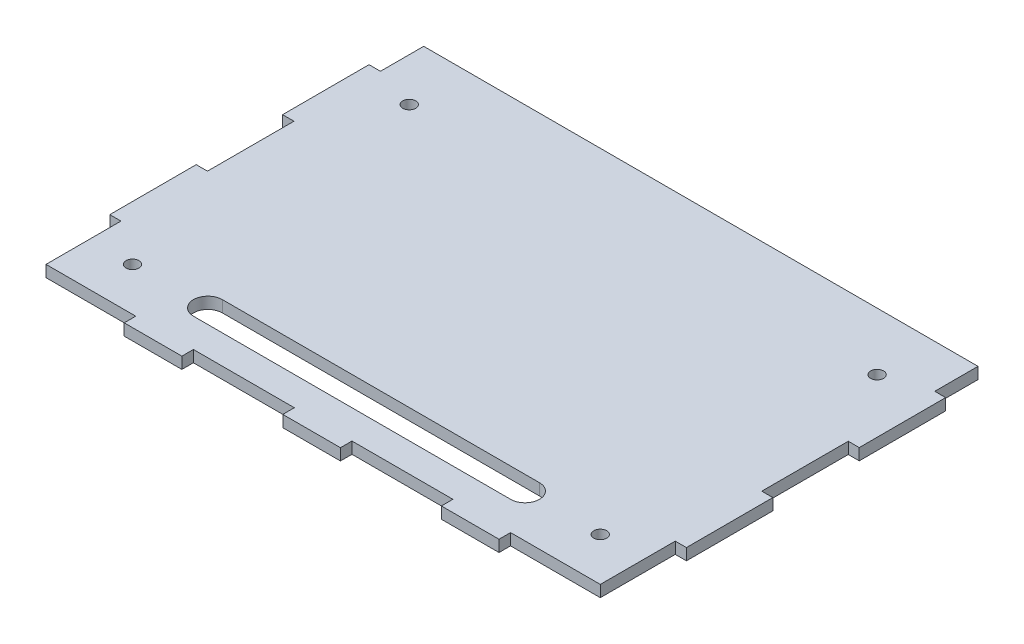
SolidWorks part; units mm, degrees
ref_plane "Plano frontal" through (0, 0, 0) normal (0, 0, 1) x (1, 0, 0)
ref_plane "Plano superior" through (0, 0, 0) normal (0, 1, 0) x (1, 0, 0)
ref_plane "Plano direito" through (0, 0, 0) normal (1, 0, 0) x (0, 0, -1)
sketch "Esboço1" plane through (0, 0, 0) normal (0, 1, 0) x (1, 0, 0)
  line L0 (-100.1571, 150) -> (-100.0001, 0)
  line L1 (-100.0001, 0) -> (100.0001, 0)
  line L2 (100.0001, 0) -> (99.843, 150)
  line L4 (99.843, 150) -> (-100.1571, 150)
  point P7 (0, 0)
  dimension "D1" = 200
  dimension "D2" = 150
extrude "Ressalto-extrusão1" add sketch "Esboço1" along normal blind 4
sketch "Esboço2" plane through (0, 4, 0) normal (0, 1, 0) x (1, 0, 0)
  line L0 (-65.0315, 0) -> (-65.0315, 4)
  line L1 (-100.0001, 0) -> (100.0001, 0) construction
  line L2 (-65.0315, 4) -> (-45.0315, 4)
  line L3 (-45.0315, 4) -> (-45.0315, 0)
  line L4 (-45.0315, 0) -> (-10.0315, 0)
  line L5 (-10.0315, 0) -> (-10.0315, 4)
  line L6 (-10.0315, 4) -> (9.9685, 4)
  line L7 (99.9685, 30) -> (99.9685, 4)
  line L8 (-100.1571, 150) -> (-100.0001, 0) construction
  line L9 (96.0942, 4) -> (99.9685, 4)
  line L10 (100.0942, 146) -> (100.0942, 150)
  line L13 (-65.0315, 4) -> (-100.0315, 4)
  line L14 (-100.0315, 4) -> (-100.0315, 0)
  line L15 (-100.0315, 0) -> (-65.0315, 0)
  line L16 (-45.0315, 4) -> (-10.0315, 4)
  line L17 (96.0942, 30) -> (96.0942, 4)
  line L22 (-100.1571, 120) -> (-96.1571, 120)
  line L23 (-96.1571, 120) -> (-96.1571, 90)
  line L24 (-96.1571, 90) -> (-100.0943, 90)
  line L25 (-100.0943, 90) -> (-100.0629, 60)
  line L26 (-100.0629, 60) -> (-96.1571, 60)
  line L27 (-96.1571, 60) -> (-96.1571, 30)
  line L31 (-100.1571, 120) -> (-100.1571, 150)
  line L32 (-100.1571, 150) -> (-96.1571, 150)
  line L33 (99.843, 150) -> (-100.1571, 150) construction
  line L34 (-96.1571, 150) -> (-96.1571, 120)
  line L35 (-96.1571, 90) -> (-96.1571, 60)
  line L36 (96.0942, 30) -> (99.9685, 30)
  line L37 (-96.1571, 30) -> (-100.0315, 30)
  line L38 (-96.1571, 30) -> (-96.1571, 4)
  line L39 (-0.0315, 150) -> (-0.0315, 0) construction
  line L41 (96.0942, 90) -> (96.0942, 60)
  line L42 (96.0942, 150) -> (96.0942, 120)
  line L49 (100.0942, 150) -> (96.0942, 150)
  line L50 (100.0942, 120) -> (100.0942, 150)
  line L51 (96.0942, 60) -> (96.0942, 30)
  line L52 (99.9999, 60) -> (96.0942, 60)
  line L53 (100.0314, 90) -> (99.9999, 60)
  line L55 (96.0942, 90) -> (100.0314, 90)
  line L57 (96.0942, 120) -> (96.0942, 90)
  line L61 (100.0942, 120) -> (96.0942, 120)
  line L62 (-100.1571, 146) -> (-100.1571, 150)
  line L63 (44.9685, 4) -> (9.9685, 4)
  line L64 (99.9685, 0) -> (64.9685, 0)
  line L65 (99.9685, 4) -> (99.9685, 0)
  line L67 (-96.1571, 4) -> (-100.0315, 4)
  line L68 (-100.0315, 30) -> (-100.0315, 4)
  line L69 (64.9685, 4) -> (99.9685, 4)
  line L70 (9.9685, 0) -> (9.9685, 4)
  line L71 (44.9685, 0) -> (9.9685, 0)
  line L72 (44.9685, 4) -> (44.9685, 0)
  line L73 (64.9685, 4) -> (44.9685, 4)
  line L74 (64.9685, 0) -> (64.9685, 4)
  point P48 (-0.0315, 4)
  line M8 (99.843, 150) -> (-100.1571, 150)
  line M9 (-100.1571, 150) -> (-100.0001, 0)
  line M10 (-100.0001, 0) -> (100.0001, 0)
  line M11 (100.0001, 0) -> (99.843, 150)
  dimension "D1" = 20
  dimension "D2" = 10
  dimension "D4" = 35
  dimension "D6" = 35
  dimension "D7" = 4
  dimension "D8" = 30
  dimension "D9" = 30
  dimension "D10" = 4
  dimension "D11" = 30
  dimension "D12" = 30
extrude "Corte-extrusão1" cut sketch "Esboço2" against normal through all contours L34 L22 M8 M9 | L35 L24 L26 M9 | L38 L37 L13 M9 | L0 L13 M9 M10 | L16 L3 L5 M10 | L72 L63 L70 M10 | L74 L65 L9 L69 M10 | L36 L17 L9 L7 | L55 L41 L52 M11 | L61 L42 M11 M8
sketch "Esboço6" plane through (0, 4, 0) normal (0, 1, 0) x (1, 0, 0)
  line L1 (96.0942, 30) -> (128.4704, 30)
  line L2 (96.0942, 30) -> (96.0942, -13.3136)
  line L3 (96.0942, -13.3136) -> (128.4704, -13.3136)
  line L4 (128.4704, 30) -> (128.4704, -13.3136)
extrude "Corte-extrusão5" cut sketch "Esboço6" against normal up to next
sketch "Esboço3" plane through (0, 4, 0) normal (0, 1, 0) x (1, 0, 0)
  line L5 (-96.1571, 150) -> (96.0942, 150)
  line L6 (-96.1571, 150) -> (-96.1571, 135)
  line L7 (-96.1571, 135) -> (96.0942, 135)
  line L8 (96.0942, 150) -> (96.0942, 135)
  dimension "D1" = 15
extrude "Corte-extrusão3" cut sketch "Esboço3" against normal through all
hole_wizard "Furo com folga de M41" positions "3DSketch1" profile "Esboço4" hole size "M4" standard "ISO" end condition through all
sketch3d "3DSketch1"
  line L0 (-65.0315, 4, -4) -> (-96.1571, 4, -4) construction
  line L1 (-96.1571, 4, -30) -> (-96.1571, 4, -4) construction
  line L2 (-96.1571, 4, -135) -> (-96.1571, 4, -120) construction
  line L3 (-96.1571, 4, -135) -> (96.0942, 4, -135) construction
  line L5 (96.0942, 4, -135) -> (96.0942, 4, -120) construction
  line L6 (96.0942, 4, -30) -> (96.0942, 4, -4) construction
  line L7 (64.9685, 4, -4) -> (96.0942, 4, -4) construction
  point P0 (-81.1571, 4, -19)
  point P2 (-81.1571, 4, -115)
  point P19 (81.0942, 4, -115)
  point P21 (81.0942, 4, -19)
  dimension "D1" = 15
  dimension "D2" = 15
  dimension "D3" = 15
  dimension "D4" = 20
  dimension "D5" = 20
  dimension "D6" = 15
  dimension "D7" = 15
  dimension "D8" = 15
sketch "Esboço4" plane through (-81.1571, 4, -19) normal (1, 0, 0) x (0, 0, 1)
  line L0 (0, 0) -> (0, 4)
  line L1 (0, 4) -> (2.25, 4)
  line L2 (2.25, 4) -> (2.25, 0)
  line L5 (2.25, 0) -> (0, 0)
  line L11 (0, -6.35) -> (0, 107.95) construction
  dimension "Thru Hole Dia." = 4.5
  dimension "Thru Hole Depth" = 4
sketch "Esboço5" plane through (0, 4, 0) normal (0, 1, 0) x (1, 0, 0)
  line L0 (-55, 19) -> (55, 19) construction
  line L1 (-55, 24) -> (55, 24)
  line L2 (-55, 14) -> (55, 14)
  line L3 (0, 134.95) -> (0, -0.05) construction
  line L4 (-81.1571, 19) -> (81.0414, 19) construction
  arc A0 (-55, 24) -> (-55, 14) centre (-55, 19) ccw
  arc A1 (55, 14) -> (55, 24) centre (55, 19) ccw
  circle A7 centre (-81.1571, 19) radius 2.25
  circle A8 centre (-81.1571, 19) radius 2.25 construction
  point P2 (0, 19)
  dimension "D2" = 5
  dimension "D1" = 110
extrude "Corte-extrusão4" cut sketch "Esboço5" against normal through all
